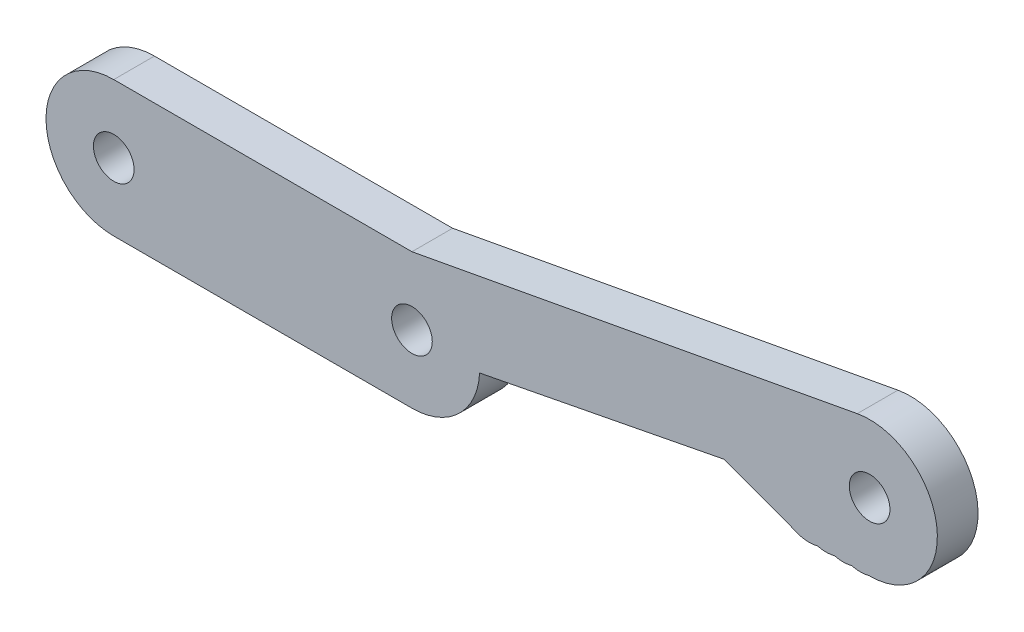
SolidWorks part; units mm, degrees
ref_plane "Piano frontale" through (0, 0, 0) normal (0, 0, 1) x (1, 0, 0)
ref_plane "Piano superiore" through (0, 0, 0) normal (0, 1, 0) x (1, 0, 0)
ref_plane "Piano destro" through (0, 0, 0) normal (1, 0, 0) x (0, 0, -1)
sketch "Schizzo1" plane through (0, 0, 0) normal (0, 0, 1) x (1, 0, 0)
  line L0 (0, 0) -> (22, 0) construction
  line L1 (0, 5) -> (22, 5)
  line L2 (0, -5) -> (22, -5)
  line L3 (22, 0) -> (55.7665, 6.1658) construction
  line L4 (22, 5) -> (54.8564, 11.0823)
  line L5 (22, 0) -> (22, -5) construction
  line L6 (22, -1.5) -> (22, -5) construction
  line L7 (22, -5) -> (22, -1.5) construction
  line L8 (22, -1.5) -> (22, -3.25) construction
  line L9 (22, 0) -> (22, -1.5) construction
  line L10 (22, 0) -> (22, -1.0038) construction
  line L11 (22, -1.0038) -> (23.1147, -1.0038) construction
  line L12 (60.7665, 6.1658) -> (60.7665, 1.1658)
  line L13 (50.6665, 1.1658) -> (60.7665, 1.1658) construction
  line L14 (55.7665, 6.1658) -> (55.7665, 4.6658) construction
  line L15 (55.7665, 6.1658) -> (55.7665, 5.1273) construction
  line L16 (55.7665, 5.1273) -> (54.6841, 5.1273) construction
  line L17 (23.1147, -1.0038) -> (54.6841, 5.1273) construction
  line L18 (50.6665, 1.1658) -> (45.0418, 3.2547)
  line L19 (45.0418, 3.2547) -> (26.9937, -0.2504)
  line L20 (55.7665, 1.1658) -> (55.7015, 1.1658)
  line L21 (53.8115, 1.1658) -> (53.8115, 1.0811) construction
  circle A0 centre (0, 0) radius 1.5
  circle A1 centre (22, 0) radius 1.5
  circle A2 centre (0, 0) radius 5
  circle A3 centre (22, 0) radius 5
  circle A4 centre (55.7665, 6.1658) radius 1.5
  circle A5 centre (55.7665, 6.1658) radius 5
  arc A6 (50.6665, 1.1658) -> (51.9215, 1.1658) centre (51.294, 3.4658) ccw
  arc A7 (51.9215, 1.1658) -> (53.1815, 1.1658) centre (52.5515, 3.4642) ccw
  arc A8 (54.4415, 1.1658) -> (53.1815, 1.1658) centre (53.8115, 3.4658) cw
  arc A9 (54.4415, 1.1658) -> (55.7015, 1.1658) centre (55.0715, 3.4658) ccw
  arc A10 (55.7015, 1.1658) -> (56.9615, 1.1658) centre (56.3315, 3.4658) ccw
  arc A11 (58.2215, 1.1658) -> (56.9615, 1.1658) centre (57.5915, 3.4658) cw
  arc A12 (58.2215, 1.1658) -> (59.4815, 1.1658) centre (58.8515, 3.4658) ccw
  arc A13 (59.4815, 1.1658) -> (60.7665, 1.1658) centre (60.124, 3.5166) ccw
  point P11 (0.0548, -1.499)
  point P12 (21.993, -1.5)
  point P13 (-0.0196, 1.4999)
  point P15 (21.993, -1.5)
  point P19 (54.8564, 11.0823)
  point P21 (51.2915, 1.1658)
  point P32 (50.6665, 1.1658)
  point P33 (52.5515, 1.1658)
  point P34 (53.1815, 1.1658)
  point P35 (53.8115, 1.1658)
  point P36 (54.4415, 1.1658)
  point P37 (55.0715, 1.1658)
  point P38 (51.9215, 1.1658)
  point P39 (55.7015, 1.1658)
  point P40 (56.3315, 1.1658)
  point P41 (56.9615, 1.1658)
  point P42 (57.5915, 1.1658)
  point P43 (58.2215, 1.1658)
  point P44 (58.8515, 1.1658)
  point P45 (59.4815, 1.1658)
  point P46 (60.1115, 1.1676)
  point P64 (51.294, 1.0817)
  point P65 (52.5515, 1.081)
  point P66 (55.0715, 1.0811)
  point P67 (53.8115, 1.0811)
  point P68 (51.2915, 1.1658)
  point P69 (56.3315, 1.0811)
  point P70 (57.5915, 1.0811)
  point P71 (58.8515, 1.0811)
  point P72 (60.124, 1.0796)
  dimension "D1" = 3
  dimension "D2" = 3
  dimension "D4" = 10
  dimension "D5" = 3.5
  dimension "D8" = 3.5002
  dimension "D9" = 3
  dimension "D10" = 10
  dimension "D42" = 32.8564
  dimension "D35" = 0.0841
  dimension "D3" = 22
  dimension "D6" = 10
  dimension "D7" = 3.5014
  dimension "D11" = 5
  dimension "D12" = 6.0038
  dimension "D13" = 10.1
  dimension "D14" = 6
  dimension "D15" = 18.0481
  dimension "D16" = 2.0889
  dimension "D17" = 4.9937
  dimension "D18" = 0.625
  dimension "D19" = 0.63
  dimension "D20" = 0.63
  dimension "D21" = 0.63
  dimension "D22" = 0.63
  dimension "D23" = 0.63
  dimension "D24" = 0.63
  dimension "D25" = 0.63
  dimension "D26" = 0.63
  dimension "D27" = 0.63
  dimension "D28" = 0.63
  dimension "D29" = 0.63
  dimension "D30" = 0.63
  dimension "D31" = 0.63
  dimension "D32" = 0.63
  dimension "D33" = 0.655
  dimension "D34" = 1.255
  dimension "D36" = 1.26
  dimension "D37" = 0.0848
  dimension "D38" = 1.26
  dimension "D39" = 0.0847
  dimension "D40" = 1.26
  dimension "D41" = 0.63
  dimension "D43" = 5
  dimension "D44" = 0.0847
  dimension "D45" = 0.63
  dimension "D46" = 1.26
  dimension "D47" = 0.0847
  dimension "D48" = 0.63
  dimension "D49" = 0.0847
  dimension "D50" = 1.26
  dimension "D51" = 0.63
  dimension "D52" = 1.26
  dimension "D53" = 0.0847
  dimension "D54" = 0.63
  dimension "D55" = 1.285
  dimension "D56" = 0.0889
  dimension "D57" = 0.6425
extrude "Estrusione-Estrusione1" add sketch "Schizzo1" along normal blind 3 contours A2 A0 | A3 L1 A2 L2 | A3 A1 | A8 A9 L20 A5 L4 A3 L19 L18 A6 A7 | A5 A4
